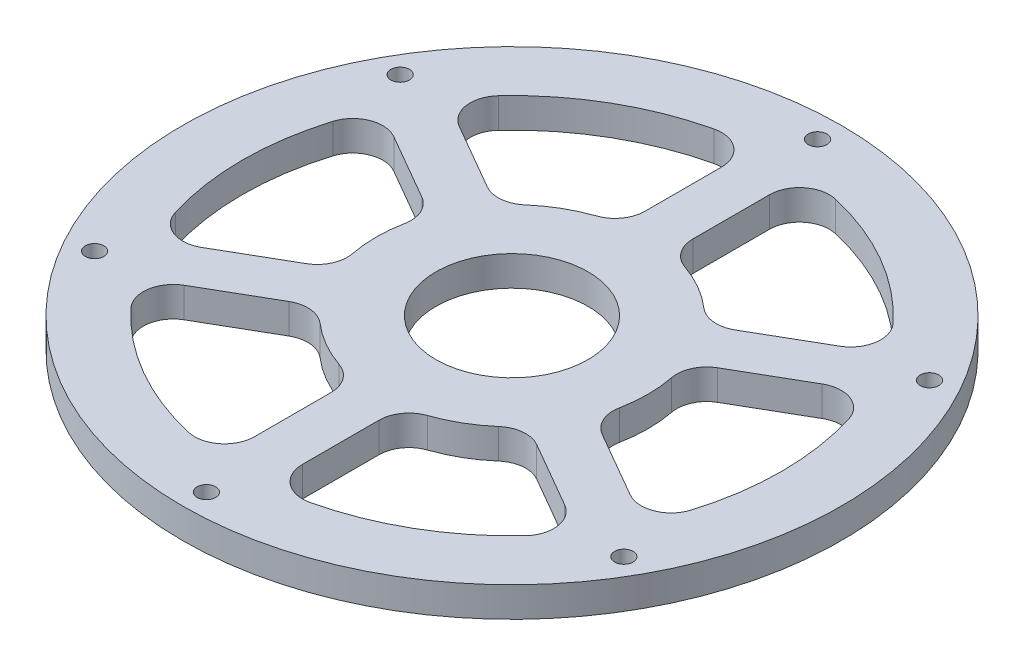
SolidWorks part; units mm, degrees
material "ABS"
ref_plane "Front Plane" through (0, 0, 0) normal (0, 0, 1) x (1, 0, 0)
ref_plane "Top Plane" through (0, 0, 0) normal (0, 1, 0) x (1, 0, 0)
ref_plane "Right Plane" through (0, 0, 0) normal (1, 0, 0) x (0, 0, -1)
sketch "Sketch1" plane through (0, 0, 0) normal (0, 1, 0) x (1, 0, 0)
  circle A0 centre (0, 0) radius 55
  dimension "D1" = 110
extrude "Boss-Extrude1" add sketch "Sketch1" along normal blind 5
sketch "Sketch2" plane through (0, 5, 0) normal (0, 1, 0) x (1, 0, 0)
  circle A0 centre (0, 0) radius 51 construction
  circle A1 centre (0, 51) radius 1.55
  circle A2 centre (44.1673, 25.5) radius 1.55
  circle A3 centre (44.1673, -25.5) radius 1.55
  circle A4 centre (0, -51) radius 1.55
  circle A5 centre (-44.1673, -25.5) radius 1.55
  circle A6 centre (-44.1673, 25.5) radius 1.55
  point P17 (0, 0)
  dimension "D1" = 102
  dimension "D2" = 3.1
  dimension "D3" = 6
extrude "Cut-Extrude1" cut sketch "Sketch2" against normal through all
sketch "Sketch5" plane through (0, 5, 0) normal (0, 1, 0) x (1, 0, 0)
  circle A0 centre (0, 0) radius 12.7
  dimension "D1" = 25.4
extrude "Cut-Extrude4" cut sketch "Sketch5" against normal through all
sketch "Sketch7" plane through (0, 5, 0) normal (0, 1, 0) x (1, 0, 0)
  line L0 (0, 45) -> (0, 0) construction
  line L1 (-4, 45) -> (-4, 22.3448)
  line L2 (4, 45) -> (4, 22.3448)
  line L3 (36.9711, 25.9641) -> (17.3512, 14.6365)
  line L4 (-4, 45) -> (-4, 0) construction
  line L5 (40.9711, 19.0359) -> (21.3512, 7.7083)
  line L6 (4, 45) -> (4, 0) construction
  line L7 (40.9711, -19.0359) -> (21.3512, -7.7083)
  line L8 (36.9711, -25.9641) -> (17.3512, -14.6365)
  line L9 (4, -45) -> (4, -22.3448)
  line L10 (-4, -45) -> (-4, -22.3448)
  line L11 (-36.9711, -25.9641) -> (-17.3512, -14.6365)
  line L12 (-40.9711, -19.0359) -> (-21.3512, -7.7083)
  line L13 (-40.9711, 19.0359) -> (-21.3512, 7.7083)
  line L14 (-36.9711, 25.9641) -> (-17.3512, 14.6365)
  circle A1 centre (0, 0) radius 22.7
  circle A2 centre (0, 0) radius 45
  circle A6 centre (0, 0) radius 12.7 construction
  circle A7 centre (0, 0) radius 55
  circle A8 centre (0, 0) radius 55
  circle A9 centre (0, 0) radius 12.7
  point P37 (0, 0)
  dimension "D1" = 0
  dimension "D2" = 10
  dimension "D3" = 10
  dimension "D4" = 4
  dimension "D5" = 4
  dimension "D6" = 6
extrude "Cut-Extrude5" cut sketch "Sketch7" against normal through all contours L13 A2 L12 A1 | L11 A2 L10 A1 | L9 A2 L8 A1 | L7 A2 L5 A1 | L3 A2 L2 A1 | L1 A2 L14 A1
fillet "Fillet1" radius 5 4 edges at (-21.3512, 2.5, 7.7083) (-21.3512, 2.5, -7.7083) (-40.8169, 2.5, 18.9468) (-40.8169, 2.5, -18.9468)
fillet "Fillet2" radius 5 20 edges at (-4, 2.5, 44.8219) (-4, 2.5, 22.3448) (-17.3512, 2.5, 14.6365) (-36.8169, 2.5, 25.875) (36.8169, 2.5, 25.875) (4, 2.5, 44.8219) (4, 2.5, 22.3448) (17.3512, 2.5, 14.6365) (40.8169, 2.5, 18.9468) (21.3512, 2.5, 7.7083) (21.3512, 2.5, -7.7083) (40.8169, 2.5, -18.9468) (36.8169, 2.5, -25.875) (4, 2.5, -44.8219) (17.3512, 2.5, -14.6365) (4, 2.5, -22.3448) (-4, 2.5, -22.3448) (-17.3512, 2.5, -14.6365) (-36.8169, 2.5, -25.875) (-4, 2.5, -44.8219)
sketch "Sketch8" plane through (0, 0, 0) normal (0, 1, 0) x (1, 0, 0)
  circle A0 centre (0, 51) radius 3.25
  dimension "D1" = 6.5
extrude "Cut-Extrude6" cut sketch "Sketch8" along normal blind 2.5
pattern_circular "CirPattern3" count 6 over 360 about axis through (0, 0, 0) along (0, 1, 0) of "Cut-Extrude6"
